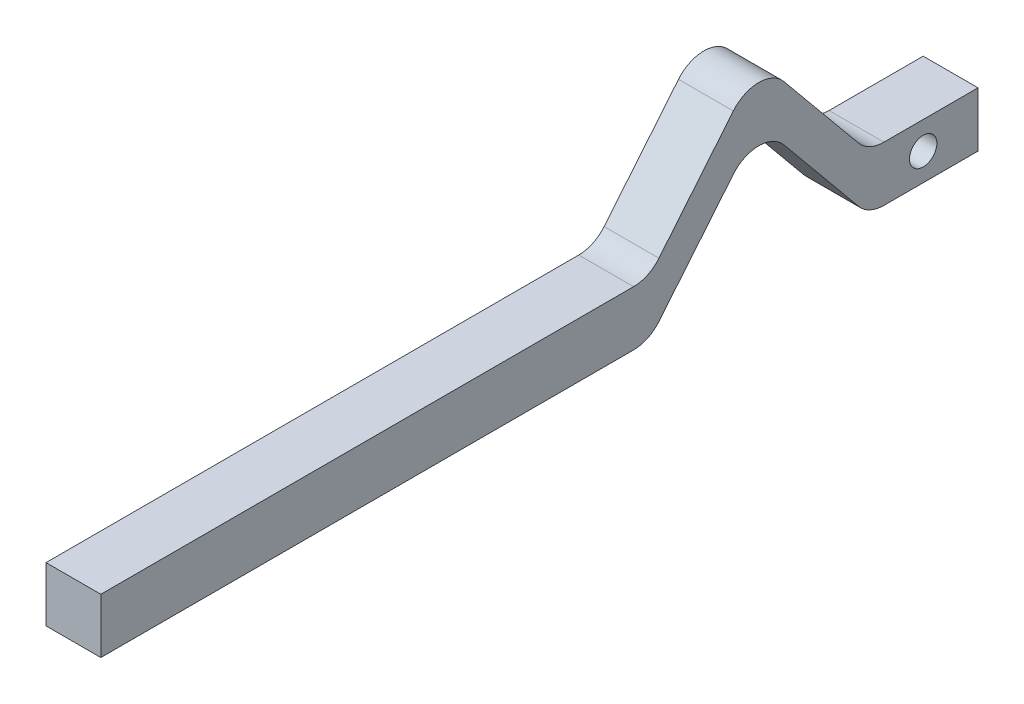
SolidWorks part; units mm, degrees
ref_plane "Front Plane" through (0, 0, 0) normal (0, 0, 1) x (1, 0, 0)
ref_plane "Top Plane" through (0, 0, 0) normal (0, 1, 0) x (1, 0, 0)
ref_plane "Right Plane" through (0, 0, 0) normal (1, 0, 0) x (0, 0, -1)
sketch "Sketch3" plane through (0, 0, 0) normal (1, 0, 0) x (0, 0, -1)
  line L0 (25.4, 6.35) -> (25.4, -6.35)
  line L1 (-101.6, -6.35) -> (101.6, -6.35)
  line L2 (-101.6, -6.35) -> (-101.6, 6.35)
  line L3 (-101.6, 6.35) -> (101.6, 6.35)
  line L4 (101.6, -6.35) -> (101.6, 6.35)
  line L5 (-101.6, -6.35) -> (101.6, 6.35) construction
  line L6 (-101.6, 6.35) -> (101.6, -6.35) construction
  line L7 (25.4, 6.35) -> (50.8, 37.1779)
  line L8 (25.4, -6.35) -> (50.8, 24.4779)
  line L9 (50.8, 37.1779) -> (50.8, 24.4779)
  line L10 (76.2, -6.35) -> (50.8, 24.4779)
  line L11 (76.2, 6.35) -> (76.2, -6.35)
  line L12 (76.2, 6.35) -> (50.8, 37.1779)
  point P0 (0, 0)
  dimension "D1" = 203.2
  dimension "D2" = 12.7
  dimension "D3" = 25.4
  dimension "D4" = 25.4
extrude "Boss-Extrude1" add sketch "Sketch3" along normal mid plane 12.7 contours L3 L11 L1 L4 | L3 L12 L9 L10 | L11 L3 L10 | L9 L7 L3 L8 | L0 L8 L3 | L3 L2 L1 L0
fillet "Fillet1" radius 7.62 6 edges at (0, -6.35, -76.2) (0, -6.35, -25.4) (0, 24.4779, -50.8) (0, 6.35, -76.2) (0, 37.1779, -50.8) (0, 6.35, -25.4)
sketch "Sketch5" plane through (6.35, 0, 0) normal (1, 0, 0) x (0, 0, -1)
  line L0 (101.6, -6.35) -> (101.6, 6.35) construction
  circle A0 centre (88.9, 0) radius 3.175
  dimension "D1" = 6.35
  dimension "D2" = 12.7
extrude "Cut-Extrude2" cut sketch "Sketch5" against normal through all
